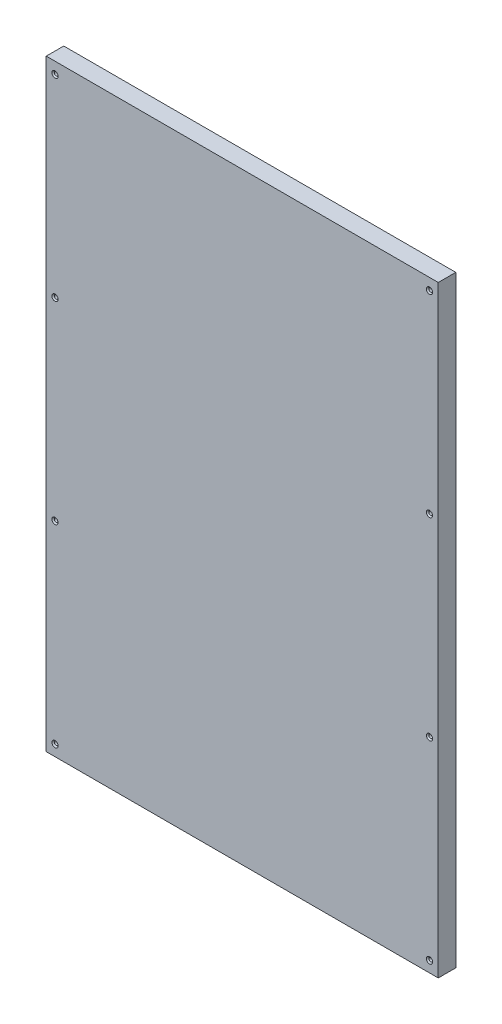
SolidWorks part; units mm, degrees
ref_plane "Front Plane" through (0, 0, 0) normal (0, 0, 1) x (1, 0, 0)
ref_plane "Top Plane" through (0, 0, 0) normal (0, 1, 0) x (1, 0, 0)
ref_plane "Right Plane" through (0, 0, 0) normal (1, 0, 0) x (0, 0, -1)
sketch "Sketch1" plane through (0, 0, 0) normal (0, 0, 1) x (1, 0, 0)
  line L1 (-178.97, 275) -> (178.97, 275)
  line L2 (-178.97, 275) -> (-178.97, -275)
  line L3 (-178.97, -275) -> (178.97, -275)
  line L4 (178.97, 275) -> (178.97, -275)
  point P4 (178.97, 0)
  point P5 (0, -275)
  dimension "D1" = 550
  dimension "D2" = 357.94
extrude "Boss-Extrude1" add sketch "Sketch1" along normal blind 16 contours L2 L3 L4 L1
hole_wizard "CSK for #4 Flat Head Machine Screw (100)1" positions "3DSketch1" profile "Sketch2" countersink size "#4" standard "ANSI Inch" end condition up to next
sketch3d "3DSketch1"
  line L0 (-178.97, -275, 16) -> (178.97, -275, 16) construction
  line L1 (-178.97, 275, 16) -> (-178.97, -275, 16) construction
  point P0 (-170.97, -265, 16)
  dimension "D1" = 10
  dimension "D2" = 8
sketch "Sketch2" plane through (-170.97, -265, 16) normal (1, 0, 0) x (0, -1, 0)
  line L0 (0, 0) -> (0, 16)
  line L1 (0, 16) -> (1.6319, 16)
  line L2 (1.6319, 16) -> (1.6319, 1.0284)
  line L3 (1.6319, 1.0284) -> (2.8575, 0)
  line L5 (2.8575, 0) -> (0, 0)
  line L6 (-1.6319, 1.0284) -> (-2.8575, 0) construction
  line L11 (0, -6.35) -> (0, 107.95) construction
  dimension "Thru Hole Dia." = 3.2639
  dimension "Thru Hole Depth" = 16
  dimension "Near C'Sink Dia." = 5.715
  dimension "Near C'Sink Angle" = 100
pattern_linear "LPattern1" count 4 spacing 176.5 along (0, 1, 0) of "CSK for #4 Flat Head Machine Screw (100)1"
mirror "Mirror1" about plane through (0, 0, 0) normal (1, 0, 0) of "LPattern1", "CSK for #4 Flat Head Machine Screw (100)1"
equation "\"Length\"= 45cm"
equation "\"Width\"= 16cm"
equation "\"Curvature radius\"= 13mm"
equation "\"Extra\"= 5cm"
equation "\"D1@Sketch1\"=\"Length\"+\"Extra\"*2"
equation "\"D2@Sketch1\"=40cm-8.29*2mm-25.48mm"
